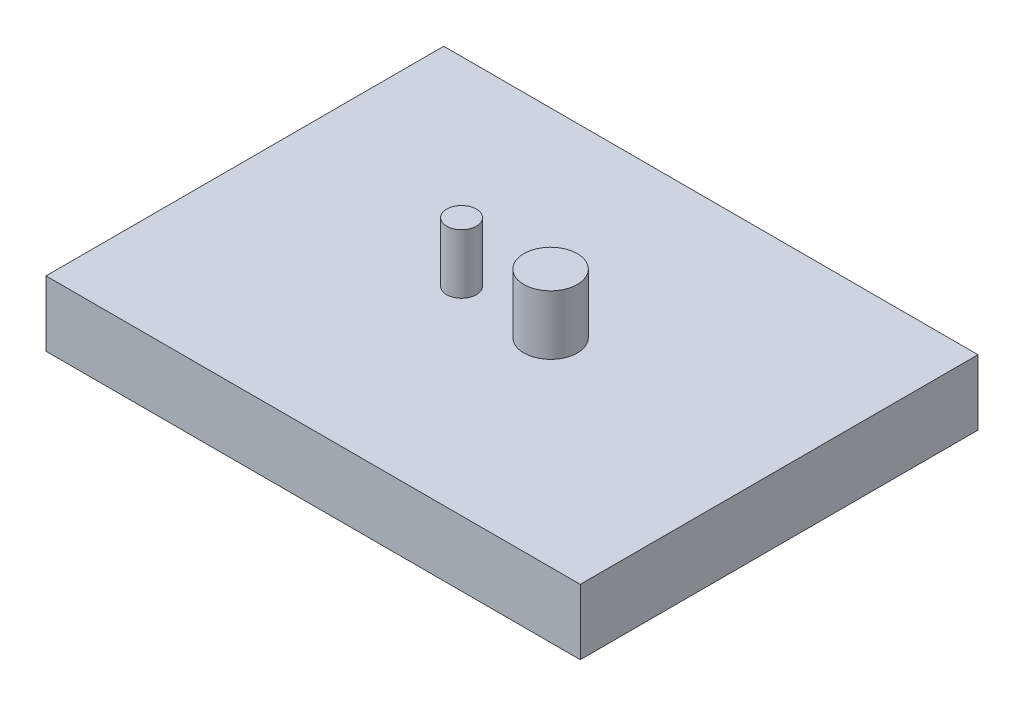
SolidWorks part; units mm, degrees
ref_plane "Спереди" through (0, 0, 0) normal (0, 0, 1) x (1, 0, 0)
ref_plane "Сверху" through (0, 0, 0) normal (0, 1, 0) x (1, 0, 0)
ref_plane "Справа" through (0, 0, 0) normal (1, 0, 0) x (0, 0, -1)
sketch "Эскиз1" plane through (0, 0, 0) normal (0, 1, 0) x (1, 0, 0)
  line L1 (0, 0) -> (90, 0)
  line L2 (0, 0) -> (0, -67)
  line L3 (0, -67) -> (90, -67)
  line L4 (90, 0) -> (90, -67)
  dimension "D1" = 90
  dimension "D2" = 67
extrude "Бобышка-Вытянуть1" add sketch "Эскиз1" along normal blind 11
sketch "Эскиз2" plane through (0, 11, 0) normal (0, 1, 0) x (1, 0, 0)
  line L0 (0, -33.5) -> (90, -33.5) construction
  line L1 (0, 0) -> (0, -67) construction
  line L2 (90, -67) -> (90, 0) construction
  line L3 (36.5, 0) -> (36.5, -67) construction
  line L4 (90, 0) -> (0, 0) construction
  line L5 (0, -67) -> (90, -67) construction
  line L6 (51.5, 0) -> (51.5, -67) construction
  circle A0 centre (36.5, -33.5) radius 2.5
  circle A1 centre (51.5, -33.5) radius 4.5
  dimension "D3" = 5
  dimension "D4" = 9
  dimension "D1" = 36.5
  dimension "D2" = 51.5
extrude "Бобышка-Вытянуть2" add sketch "Эскиз2" along normal blind 10
